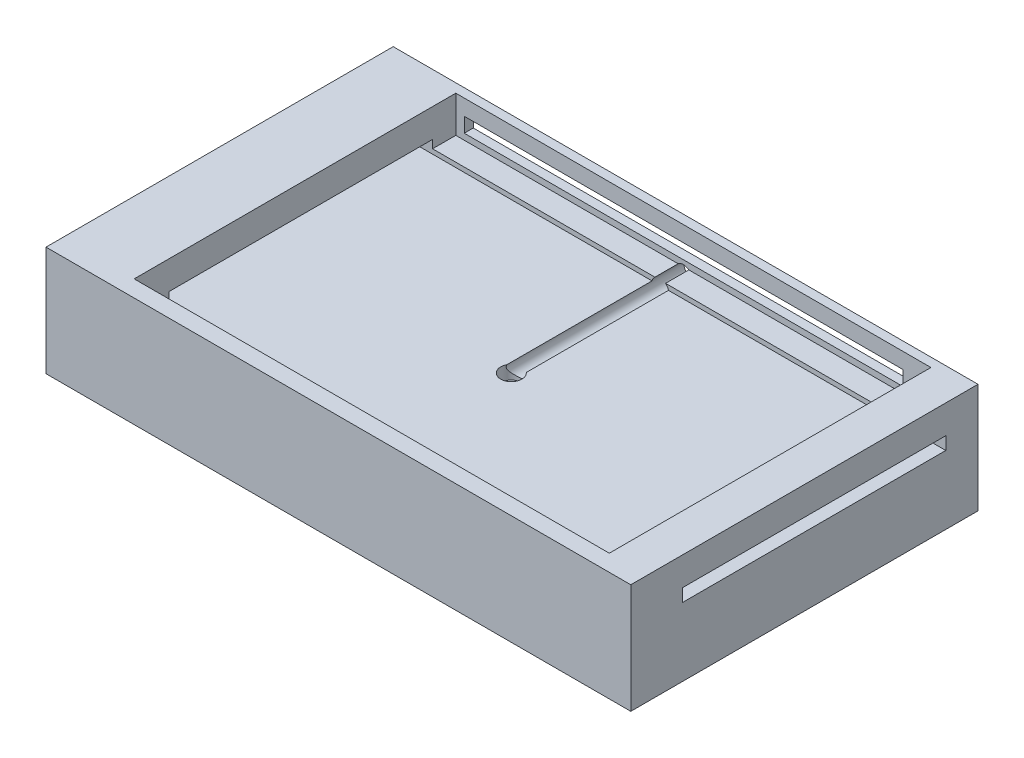
SolidWorks part; units mm, degrees
ref_plane "Front Plane" through (0, 0, 0) normal (0, 0, 1) x (1, 0, 0)
ref_plane "Top Plane" through (0, 0, 0) normal (0, 1, 0) x (1, 0, 0)
ref_plane "Right Plane" through (0, 0, 0) normal (1, 0, 0) x (0, 0, -1)
sketch "Sketch1" plane through (0, 0, 0) normal (0, 1, 0) x (1, 0, 0)
  line L1 (-80.2367, 33.0225) -> (79.7633, 33.0225)
  line L2 (-80.2367, 33.0225) -> (-80.2367, -61.9775)
  line L3 (-80.2367, -61.9775) -> (79.7633, -61.9775)
  line L4 (79.7633, 33.0225) -> (79.7633, -61.9775)
  dimension "D1" = 160
  dimension "D2" = 95
extrude "Boss-Extrude1" add sketch "Sketch1" along normal blind 30
sketch "Sketch3" plane through (0, 30, 0) normal (0, 1, 0) x (1, 0, 0)
  line L1 (-60.6526, -57.4409) -> (69.3474, -57.4409)
  line L2 (-60.6526, -57.4409) -> (-60.6526, 30.5591)
  line L3 (-60.6526, 30.5591) -> (69.3474, 30.5591)
  line L4 (69.3474, -57.4409) -> (69.3474, 30.5591)
  line L5 (-60.6526, -57.4409) -> (69.3474, 30.5591) construction
  line L6 (-60.6526, 30.5591) -> (69.3474, -57.4409) construction
  point P0 (4.3474, -13.4409)
  dimension "D1" = 88
  dimension "D2" = 130
extrude "Cut-Extrude1" cut sketch "Sketch3" against normal blind 10
sketch "Sketch4" plane through (0, 0, -33.0225) normal (0, 0, -1) x (-1, 0, 0)
  line L1 (-61.774, 21.6735) -> (58.3343, 21.6735)
  line L2 (-61.774, 21.6735) -> (-61.774, 25.6912)
  line L3 (-61.774, 25.6912) -> (58.3343, 25.6912)
  line L4 (58.3343, 21.6735) -> (58.3343, 25.6912)
  line L5 (-61.774, 21.6735) -> (58.3343, 25.6912) construction
  line L6 (-61.774, 25.6912) -> (58.3343, 21.6735) construction
  point P0 (-1.7199, 23.6824)
  dimension "D1" = 4.0177
  dimension "D2" = 120.1083
extrude "Cut-Extrude2" cut sketch "Sketch4" against normal blind 5
sketch "Sketch6" plane through (79.7633, 0, 0) normal (1, 0, 0) x (0, 0, -1)
  line L1 (-47.8531, 22.2226) -> (24.2063, 22.2226)
  line L2 (-47.8531, 22.2226) -> (-47.8531, 18.7226)
  line L3 (-47.8531, 18.7226) -> (24.2063, 18.7226)
  line L4 (24.2063, 22.2226) -> (24.2063, 18.7226)
  dimension "D1" = 3.5
  dimension "D2" = 72.0594
extrude "Cut-Extrude4" cut sketch "Sketch6" along direction (1, 0, 0) on the side against the normal through all both and the other way through all from offset 10
sketch "Sketch7" plane through (-65.1875, 5.7891, -33.0225) normal (0, 0, -1) x (-1, 0, 0)
  circle A0 centre (-66.8247, 12.4351) radius 2.3
  point P2 (-66.8247, 12.4351)
extrude "Cut-Extrude5" cut sketch "Sketch7" against normal blind 50
sketch "Sketch8" plane through (0, 20, 0) normal (0, 1, 0) x (1, 0, 0)
  circle A0 centre (1.9665, -16.8752) radius 2.9072
extrude "Cut-Extrude6" cut sketch "Sketch8" against normal blind 5
